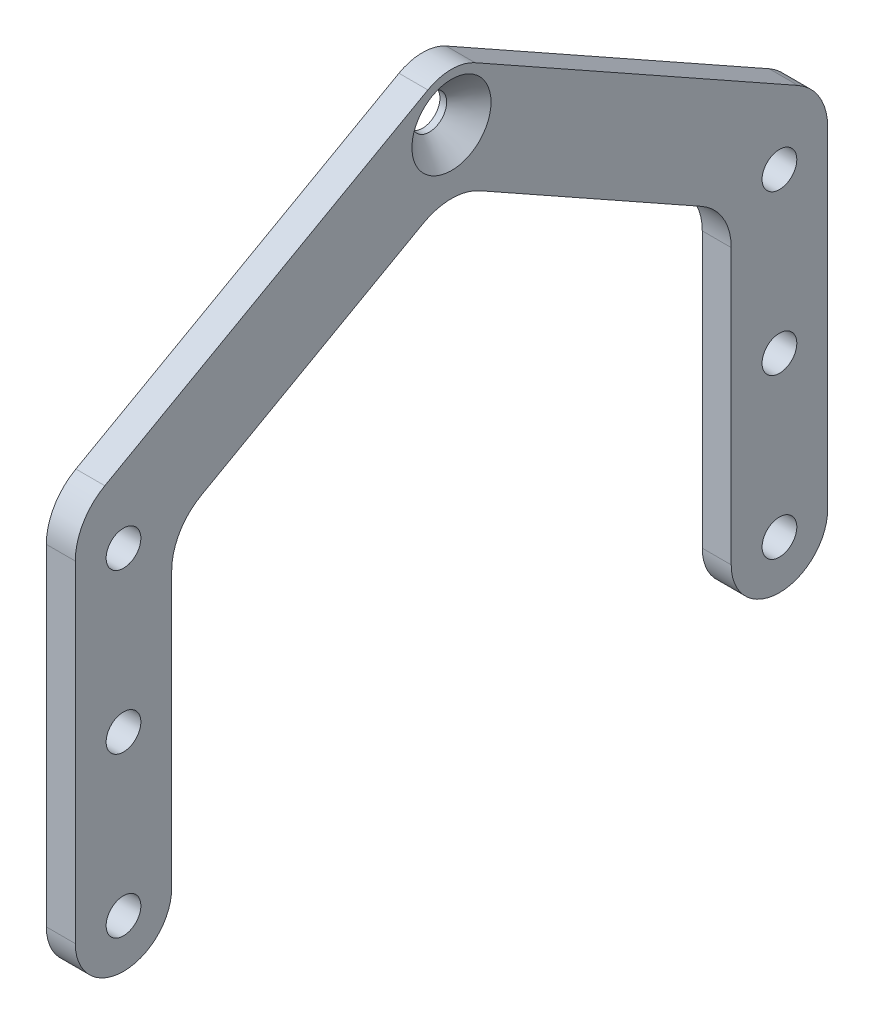
SolidWorks part; units mm, degrees
ref_plane "前视基准面" through (0, 0, 0) normal (0, 0, 1) x (1, 0, 0)
ref_plane "上视基准面" through (0, 0, 0) normal (0, 1, 0) x (1, 0, 0)
ref_plane "右视基准面" through (0, 0, 0) normal (1, 0, 0) x (0, 0, -1)
sketch "草图1" plane through (0, 0, 0) normal (1, 0, 0) x (0, 0, -1)
  line L0 (0, 39.2639) -> (0, 0) construction
  line L1 (-17, 0) -> (17, 0) construction
  line L2 (-14.5, 0) -> (-14.5, 16)
  line L3 (-19.5, 0) -> (-19.5, 18.9282)
  line L4 (14.5, 0) -> (14.5, 16)
  line L5 (19.5, 0) -> (19.5, 18.9282)
  line L6 (-19.5, 18.9282) -> (-1.2231, 29.1804)
  line L7 (-14.5, 16) -> (0, 24.1335)
  line L8 (0, 24.1335) -> (14.5, 16)
  line L9 (1.2231, 29.1804) -> (19.5, 18.9282)
  circle A0 centre (-17, 0) radius 0.9
  circle A1 centre (17, 0) radius 0.9
  circle A2 centre (0, 27) radius 0.9
  arc A3 (-19.5, 0) -> (-14.5, 0) centre (-17, 0) ccw
  arc A4 (14.5, 0) -> (19.5, 0) centre (17, 0) ccw
  arc A5 (1.2231, 29.1804) -> (-1.2231, 29.1804) centre (0, 27) ccw
  dimension "D1" = 1.8
  dimension "D4" = 5
  dimension "D2" = 34
  dimension "D3" = 27
  dimension "D5" = 16
  dimension "D6" = 17
extrude "凸台-拉伸1" add sketch "草图1" along normal blind 1.5
fillet "圆角1" radius 3 5 edges at (0.75, 16, 14.5) (0.75, 18.9282, 19.5) (0.75, 18.9282, -19.5) (0.75, 16, -14.5) (0.75, 24.1335, 0)
sketch "草图2" plane through (1.5, 0, 0) normal (1, 0, 0) x (0, 0, -1)
  line L0 (-17, 16.5) -> (-17, 0) construction
  line L1 (0, 30.029) -> (0, 0) construction
  circle A0 centre (-17, 16.5) radius 0.9
  circle A1 centre (-17, 8.25) radius 0.9
  circle A2 centre (17, 8.25) radius 0.9
  circle A3 centre (17, 16.5) radius 0.9
  dimension "D1" = 1.8
  dimension "D2" = 16.5
  dimension "D3" = 8.25
extrude "切除-拉伸1" cut sketch "草图2" against normal blind 10
hole_wizard "M2 平头机械螺钉的锥形沉头孔1" positions "3D草图1" profile "草图3" countersink size "M2" standard "ANSI Metric" end condition through all
sketch3d "3D草图1"
  line L0 (1.5, 27, 0) -> (0, 27, 0) construction
  point P0 (1.5, 27, 0)
sketch "草图3" plane through (1.5, 27, 0) normal (0, 1, 0) x (0, 0, -1)
  line L0 (0, 0) -> (0, 1.5)
  line L1 (0, 1.5) -> (0.85, 1.5)
  line L2 (0.85, 1.5) -> (0.85, 1.2)
  line L3 (0.85, 1.2) -> (2.05, 0)
  line L5 (2.05, 0) -> (0, 0)
  line L6 (-0.85, 1.2) -> (-2.05, 0) construction
  line L11 (0, -6.35) -> (0, 107.95) construction
  dimension "通孔孔直径" = 1.7
  dimension "通孔孔深度" = 1.5
  dimension "近端锥形沉头孔直径" = 4.1
  dimension "近端锥形沉头孔角度" = 90
